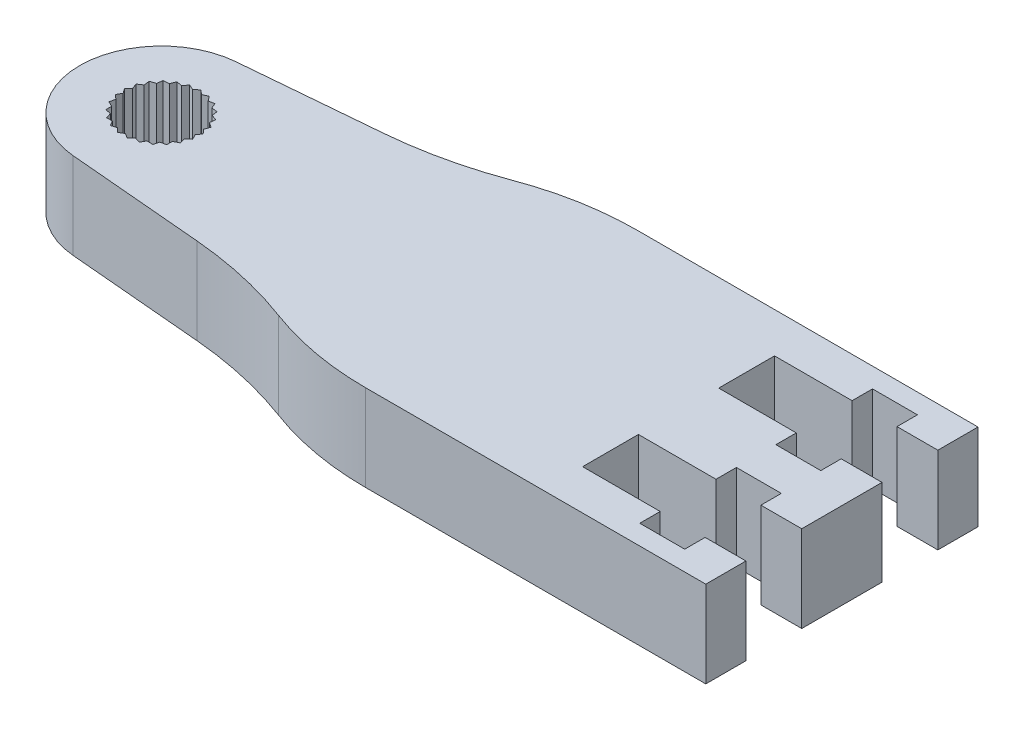
SolidWorks part; units mm, degrees
ref_plane "Front Plane" through (0, 0, 0) normal (0, 0, 1) x (1, 0, 0)
ref_plane "Top Plane" through (0, 0, 0) normal (0, 1, 0) x (1, 0, 0)
ref_plane "Right Plane" through (0, 0, 0) normal (1, 0, 0) x (0, 0, -1)
sketch "Sketch1" plane through (0, 0, 0) normal (0, 1, 0) x (1, 0, 0)
  line L0 (0, 2.895) -> (-0.3321, 2.6291)
  line L1 (0, 2.895) -> (0.3321, 2.6291)
  line L2 (0.72, 2.804) -> (0.3321, 2.6291)
  line L3 (0.72, 2.804) -> (0.9755, 2.4639)
  line L4 (1.3947, 2.5369) -> (0.9755, 2.4639)
  line L5 (1.3947, 2.5369) -> (1.5576, 2.1439)
  line L6 (1.9818, 2.1104) -> (1.5576, 2.1439)
  line L7 (1.9818, 2.1104) -> (2.0419, 1.6892)
  line L8 (2.4443, 1.5512) -> (2.0419, 1.6892)
  line L9 (2.4443, 1.5512) -> (2.3978, 1.1283)
  line L10 (2.7533, 0.8946) -> (2.3978, 1.1283)
  line L11 (2.7533, 0.8946) -> (2.6031, 0.4966)
  line L12 (2.8893, 0.1818) -> (2.6031, 0.4966)
  line L13 (2.8893, 0.1818) -> (2.6448, -0.1664)
  line L14 (2.8437, -0.5425) -> (2.6448, -0.1664)
  line L15 (2.8437, -0.5425) -> (2.5203, -0.8189)
  line L16 (2.6195, -1.2326) -> (2.5203, -0.8189)
  line L17 (2.6195, -1.2326) -> (2.2375, -1.4199)
  line L18 (2.2306, -1.8453) -> (2.2375, -1.4199)
  line L19 (2.2306, -1.8453) -> (1.814, -1.9318)
  line L20 (1.7016, -2.3421) -> (1.814, -1.9318)
  line L21 (1.7016, -2.3421) -> (1.2766, -2.3222)
  line L22 (1.0657, -2.6917) -> (1.2766, -2.3222)
  line L23 (1.0657, -2.6917) -> (0.659, -2.5667)
  line L24 (0.3628, -2.8722) -> (0.659, -2.5667)
  line L25 (0.3628, -2.8722) -> (0, -2.65)
  line L26 (-0.3628, -2.8722) -> (0, -2.65)
  line L27 (-0.3628, -2.8722) -> (-0.659, -2.5667)
  line L28 (-1.0657, -2.6917) -> (-0.659, -2.5667)
  line L29 (-1.0657, -2.6917) -> (-1.2766, -2.3222)
  line L30 (-1.7016, -2.3421) -> (-1.2766, -2.3222)
  line L31 (-1.7016, -2.3421) -> (-1.814, -1.9318)
  line L32 (-2.2306, -1.8453) -> (-1.814, -1.9318)
  line L33 (-2.2306, -1.8453) -> (-2.2375, -1.4199)
  line L34 (-2.6195, -1.2326) -> (-2.2375, -1.4199)
  line L35 (-2.6195, -1.2326) -> (-2.5203, -0.8189)
  line L36 (-2.8437, -0.5425) -> (-2.5203, -0.8189)
  line L37 (-2.8437, -0.5425) -> (-2.6448, -0.1664)
  line L38 (-2.8893, 0.1818) -> (-2.6448, -0.1664)
  line L39 (-2.8893, 0.1818) -> (-2.6031, 0.4966)
  line L40 (-2.7533, 0.8946) -> (-2.6031, 0.4966)
  line L41 (-2.7533, 0.8946) -> (-2.3978, 1.1283)
  line L42 (-2.4443, 1.5512) -> (-2.3978, 1.1283)
  line L43 (-2.4443, 1.5512) -> (-2.0419, 1.6892)
  line L44 (-1.9818, 2.1104) -> (-2.0419, 1.6892)
  line L45 (-1.9818, 2.1104) -> (-1.5576, 2.1439)
  line L46 (-1.3947, 2.5369) -> (-1.5576, 2.1439)
  line L47 (-1.3947, 2.5369) -> (-0.9755, 2.4639)
  line L48 (-0.72, 2.804) -> (-0.9755, 2.4639)
  line L49 (-0.72, 2.804) -> (-0.3321, 2.6291)
  line L52 (0, 0) -> (50, 0) construction
  line L74 (50, -10) -> (50, -7.05)
  line L79 (9.4771, 6.8521) -> (-0.5229, 5.9772)
  line L81 (9.4771, -6.8521) -> (-0.5229, -5.9772)
  line L93 (50, 10) -> (25, 10)
  line L106 (50, -10) -> (25, -10)
  line L109 (50, 5) -> (25, 5) construction
  line L110 (50, 7.05) -> (47, 7.05)
  line L111 (47, 7.05) -> (47, 8.55)
  line L112 (47, 8.55) -> (43.7, 8.55)
  line L113 (43.7, 8.55) -> (43.7, 7.05)
  line L114 (43.7, 7.05) -> (38, 7.05)
  line L115 (38, 7.05) -> (38, 2.95)
  line L117 (43.7, 2.95) -> (38, 2.95)
  line L118 (50, -2.95) -> (50, 2.95)
  line L121 (43.7, 1.45) -> (43.7, 2.95)
  line L122 (47, 1.45) -> (43.7, 1.45)
  line L123 (47, 2.95) -> (47, 1.45)
  line L124 (50, 2.95) -> (47, 2.95)
  line L125 (50, 7.05) -> (50, 10)
  line L126 (50, -2.95) -> (47, -2.95)
  line L127 (47, -2.95) -> (47, -1.45)
  line L128 (47, -1.45) -> (43.7, -1.45)
  line L129 (43.7, -1.45) -> (43.7, -2.95)
  line L130 (43.7, -2.95) -> (38, -2.95)
  line L131 (38, -7.05) -> (38, -2.95)
  line L132 (43.7, -7.05) -> (38, -7.05)
  line L133 (43.7, -8.55) -> (43.7, -7.05)
  line L134 (47, -8.55) -> (43.7, -8.55)
  line L135 (47, -7.05) -> (47, -8.55)
  line L136 (50, -7.05) -> (47, -7.05)
  circle A0 centre (0, 0) radius 2.895 construction
  circle A1 centre (0, 0) radius 2.65 construction
  arc A4 (-0.5229, 5.9772) -> (-0.5229, -5.9772) centre (0, 0) ccw
  arc A5 (25, 10) -> (17.213, 8.5972) centre (25, -12.3138) ccw
  arc A6 (17.213, 8.5972) -> (9.4771, 6.8521) centre (6.9019, 36.2866) cw
  arc A7 (25, -10) -> (17.213, -8.5972) centre (25, 12.3138) cw
  arc A8 (17.213, -8.5972) -> (9.4771, -6.8521) centre (6.9019, -36.2866) ccw
  point P6 (0, 0)
  point P17 (50, 0)
  point P32 (34.3162, 10)
  point P38 (49.5385, 10)
  point P41 (14.2454, 8.1166)
  point P44 (0, 0)
  point P50 (38, 5)
  point P77 (31.554, 10)
  point P82 (0, 0)
  point P83 (0, 0)
  point P84 (50, 0)
  point P86 (46.0407, 5)
  point P87 (0, 0)
  point P88 (35.1949, 5)
  point P89 (0, 0)
  dimension "D1" = 5.79
  dimension "D2" = 5.3
  dimension "D4" = 12
  dimension "D5" = 50
  dimension "D6" = 20
  dimension "D7" = 25
  dimension "D9" = 10
  dimension "D8" = 5
  dimension "D10" = 5
  dimension "D11" = 12
  dimension "D12" = 3.3
  dimension "D13" = 3
  dimension "D14" = 7.1
  dimension "D15" = 4.1
  dimension "D3" = 25
extrude "Boss-Extrude1" add sketch "Sketch1" along normal blind 6.35
